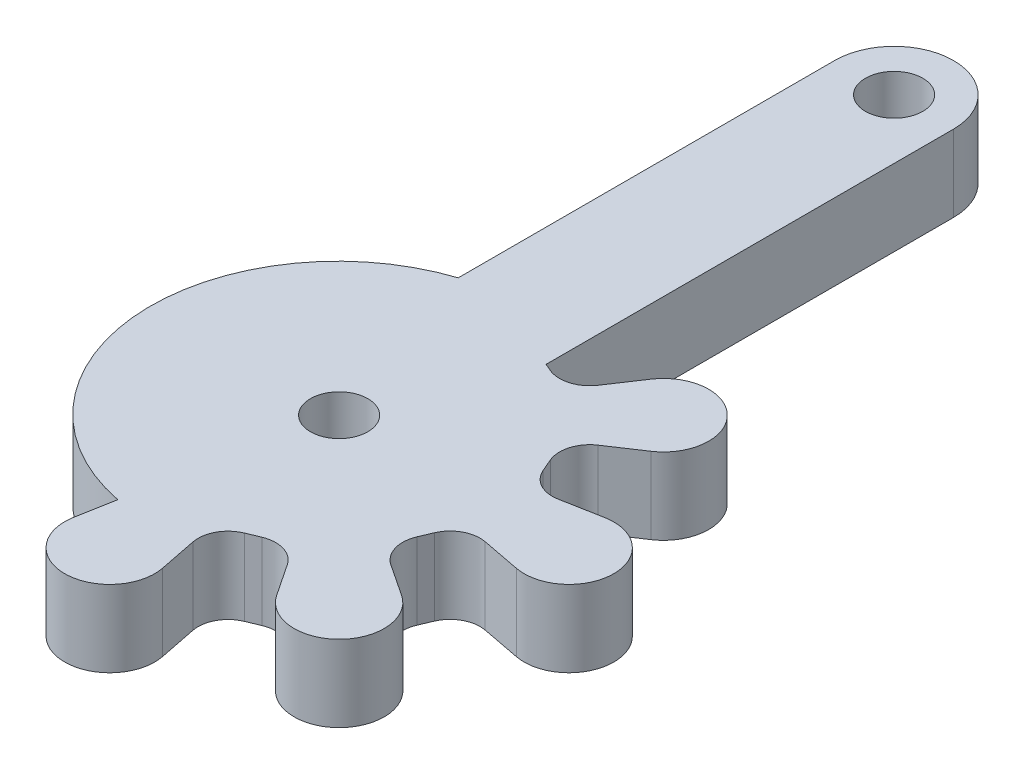
SolidWorks part; units mm, degrees
ref_plane "Alzado" through (0, 0, 0) normal (0, 0, 1) x (1, 0, 0)
ref_plane "Planta" through (0, 0, 0) normal (0, 1, 0) x (1, 0, 0)
ref_plane "Vista lateral" through (0, 0, 0) normal (1, 0, 0) x (0, 0, -1)
sketch "Croquis1" plane through (0, 0, 0) normal (0, 1, 0) x (1, 0, 0)
  line L0 (-4.8427, 0.572) -> (-4.8427, 20.2426)
  line L1 (1.3673, 20.2426) -> (1.3673, -1.0487)
  line L2 (1.3673, -1.0487) -> (1.6693, -1.1773)
  line L3 (1.1144, -16.5645) -> (1.763, -16.2951)
  line L4 (3.671, -16.8741) -> (4.7805, -18.5391)
  line L5 (3.6753, -0.6351) -> (4.7812, 1.0259)
  line L6 (-3.6983, -18.3635) -> (-4.0539, -20.3263)
  line L7 (0.1777, -18.3218) -> (0.5705, -20.2839)
  line L8 (6.3895, -14.1794) -> (8.0386, -15.2709)
  line L9 (7.803, -10.6661) -> (9.8262, -11.0544)
  line L10 (7.7832, -6.8335) -> (9.8371, -6.4493)
  line L11 (6.3808, -3.347) -> (8.0459, -2.2375)
  line L12 (6.0915, -5.9306) -> (5.8089, -5.2717)
  line L13 (5.8001, -12.2233) -> (6.0676, -11.592)
  arc A0 (1.3673, 20.2426) -> (-4.8427, 20.2426) centre (-1.7377, 20.2426) ccw
  circle A1 centre (-1.7377, 20.2426) radius 1.5
  circle A2 centre (-1.7377, -8.7574) radius 1.5
  arc A3 (-4.8427, 0.572) -> (-3.6983, -18.3635) centre (-1.8088, -8.747) ccw
  arc A4 (8.0459, -2.2375) -> (4.7812, 1.0259) centre (6.7406, -0.2786) ccw
  arc A5 (4.7805, -18.5391) -> (8.0386, -15.2709) centre (6.7394, -17.2338) ccw
  arc A6 (-4.0539, -20.3263) -> (0.5705, -20.2839) centre (-1.7377, -20.746) ccw
  arc A7 (1.1144, -16.5645) -> (0.1777, -18.3218) centre (1.7165, -18.0137) ccw
  arc A8 (3.671, -16.8741) -> (1.763, -16.2951) centre (2.3651, -17.7443) ccw
  arc A9 (1.6693, -1.1773) -> (3.6753, -0.6351) centre (2.3629, 0.2386) ccw
  arc A10 (6.3809, -3.347) -> (5.8089, -5.2717) centre (7.2511, -4.6529) ccw
  arc A11 (6.0915, -5.9306) -> (7.7832, -6.8335) centre (7.5012, -5.3258) ccw
  arc A12 (5.8001, -12.2233) -> (6.3895, -14.1794) centre (7.2714, -12.8469) ccw
  arc A13 (7.803, -10.6661) -> (6.0676, -11.592) centre (7.5081, -12.2025) ccw
  arc A14 (9.8262, -11.0544) -> (9.8371, -6.4493) centre (10.268, -8.7529) ccw
extrude "Saliente-Extruir1" add sketch "Croquis1" along normal blind 4 contours L9 A14 L10 A11 L12 A10 L11 A4 L5 A9 L2 L1 A0 L0 A3 L6 A6 L7 A7 L3 A8 L4 A5 L8 A12 L13 A13 A1 A2
